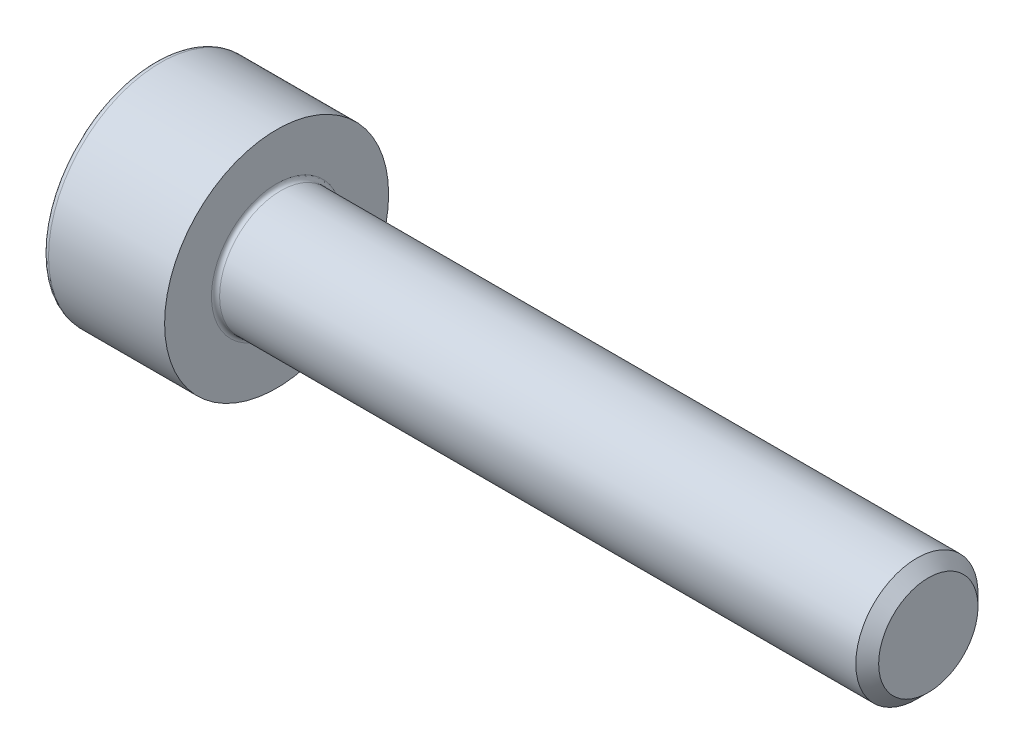
SolidWorks part; units mm, degrees
revolve "Base-Revolve" add sketch "BodySke"
sketch "BodySke" plane through (0, 0, 0) normal (0, 0, 1) x (1, 0, 0)
  line L0 (0, 0) -> (0, 2.75)
  line L1 (0, 2.75) -> (3, 2.75)
  line L2 (3, 2.75) -> (3, 1.5)
  line L3 (3, 1.5) -> (18.7195, 1.5)
  line L4 (19, 1.2195) -> (19, 0)
  line L5 (19, 0) -> (0, 0)
  line L6 (-31.75, 0) -> (127, 0) construction
  line L8 (19, 1.2195) -> (18.7195, 1.5)
  line L10 (19, -1.2195) -> (18.7195, -1.5) construction
  line L11 (3.5, 9.525) -> (3.5, 3.175) construction
  line L12 (3, 9.525) -> (3, 3.175) construction
  line L13 (-41, 9.525) -> (-41, 3.175) construction
  dimension "Head_ht" = 3
  dimension "Length" = 16
  dimension "Body_ch_ang" = 45
  dimension "Diameter" = 3
  dimension "Minor_dia" = 2.439
  dimension "Advance" = 0.5
  dimension "Thread_nom" = 16
  dimension "Thread_length" = 60
  dimension "Head_dia" = 5.5
cosmetic thread "ThreadCosmetic" [suppressed]
fillet "Fillet1" radius 0.1 1 edges at (3, 0, 1.5)
fillet "Fillet2" radius 0.15 1 edges at (0, 0, 2.75)
ref_plane "Plane1" through (0, 0, 0) normal (0, 0, 1) x (1, 0, 0)
ref_plane "Plane2" through (0, 0, 0) normal (0, 1, 0) x (1, 0, 0)
ref_plane "Plane3" through (0, 0, 0) normal (1, 0, 0) x (0, 0, -1)
sketch "Sketch2" plane through (0, 0, 0) normal (0, 0, 1) x (1, 0, 0)
  line L0 (0, 1.28) -> (1.3, 1.28)
  line L1 (1.3, 1.28) -> (2.039, 0)
  line L2 (-31.75, 0) -> (127, 0) construction
  line L3 (2.039, 0) -> (0, 0)
  line L4 (0, 0) -> (0, 1.28)
  line L6 (0, 0) -> (47.625, 0) construction
  dimension "D1" = 1.28
  dimension "D2" = 60
  dimension "Depth" = 1.3
revolve "Hex-PreBroach" cut sketch "Sketch2" angle 360 about L6
sketch "Sketch3" plane through (0, 0, 0) normal (-1, 0, 0) x (0, 0.5, 0.866)
  line L0 (0.739, 1.28) -> (-0.739, 1.28)
  line L1 (-0.739, 1.28) -> (-1.478, 0)
  line L2 (0.739, 1.28) -> (1.478, 0)
  line L3 (0.739, -1.28) -> (1.478, 0)
  line L4 (0.739, -1.28) -> (-0.739, -1.28)
  line L5 (-0.739, -1.28) -> (-1.478, 0)
  dimension "D1" = 1.28
  dimension "D2" = 1.28
  dimension "Hex_size" = 2.56
extrude "Hex" cut sketch "Sketch3" against normal blind 1.3
sketch "ThdSchSke" plane through (0, 0, 0) normal (0, 0, 1) x (1, 0, 0)
  line L0 (4.5, -1.2195) -> (4.3036, -1.5)
  line L1 (4.5, -1.2195) -> (4.6964, -1.5)
  line L2 (4.6964, -1.5) -> (4.6964, -1.875)
  line L3 (-3.175, 0) -> (5.1513, 0) construction
  line L4 (0, 2.6) -> (0, -2.6) construction
  line L5 (4.6964, -1.875) -> (4.3036, -1.875)
  line L6 (4.3036, -1.875) -> (4.3036, -1.5)
  dimension "Thread_minor" = 2.439
  dimension "Diameter" = 3
  dimension "Start" = 4.5
revolve "ThreadSchematic" [suppressed] cut sketch "ThdSchSke" angle 360 about L3
pattern_linear "ThdSchPat" [suppressed]
equation "\"D2@Sketch3\" = \"Hex_size@Sketch3\" / 2"
equation "\"D1@Sketch3\" = \"Hex_size@Sketch3\" / 2"
equation "\"D1@Sketch2\" = \"Hex_size@Sketch3\" / 2"
equation "\"Thread_minor@ThreadCosmetic\"  =  \"Minor_dia@BodySke\""
equation "\"Depth@Sketch2\" =  \"Key_eng@Hex\""
equation "\"Thread_length@ThreadCosmetic\" = ((sgn( (\"Length@BodySke\" - \"Advance@BodySke\" * 3.0) - \"Thread_nom@BodySke\" )-1)*( (\"Length@BodySke\" - \"Advance@BodySke\" * 3.0) - \"Thread_nom@BodySke\" ))/-2+ \"Thread_nom@BodySke\""
equation "\"Thread_minor@ThdSchSke\" = \"Minor_dia@BodySke\""
equation "\"Diameter@ThdSchSke\" = \"Diameter@BodySke\""
equation "\"Overcut@ThdSchSke\" = \"Diameter@BodySke\" * 1.25"
equation "\"Start@ThdSchSke\" = \"Head_ht@BodySke\" + \"Length@BodySke\" - \"Thread_length@ThreadCosmetic\"  '---Non-countersunk---"
equation "\"Num_threads@ThdSchPat\" = int( \"Thread_length@ThreadCosmetic\" / \"Advance@BodySke\" + 0.999 )  + 1"
equation "\"Advance@ThdSchPat\" = \"Thread_length@ThreadCosmetic\" /  (\"Num_threads@ThdSchPat\" - 1) 'relax it"
equation "\"Num_threads@ThdSchPat\" = \"Num_threads@ThdSchPat\" - sgn( \"Num_threads@ThdSchPat\" - 1) '---chamfered tips only---"
